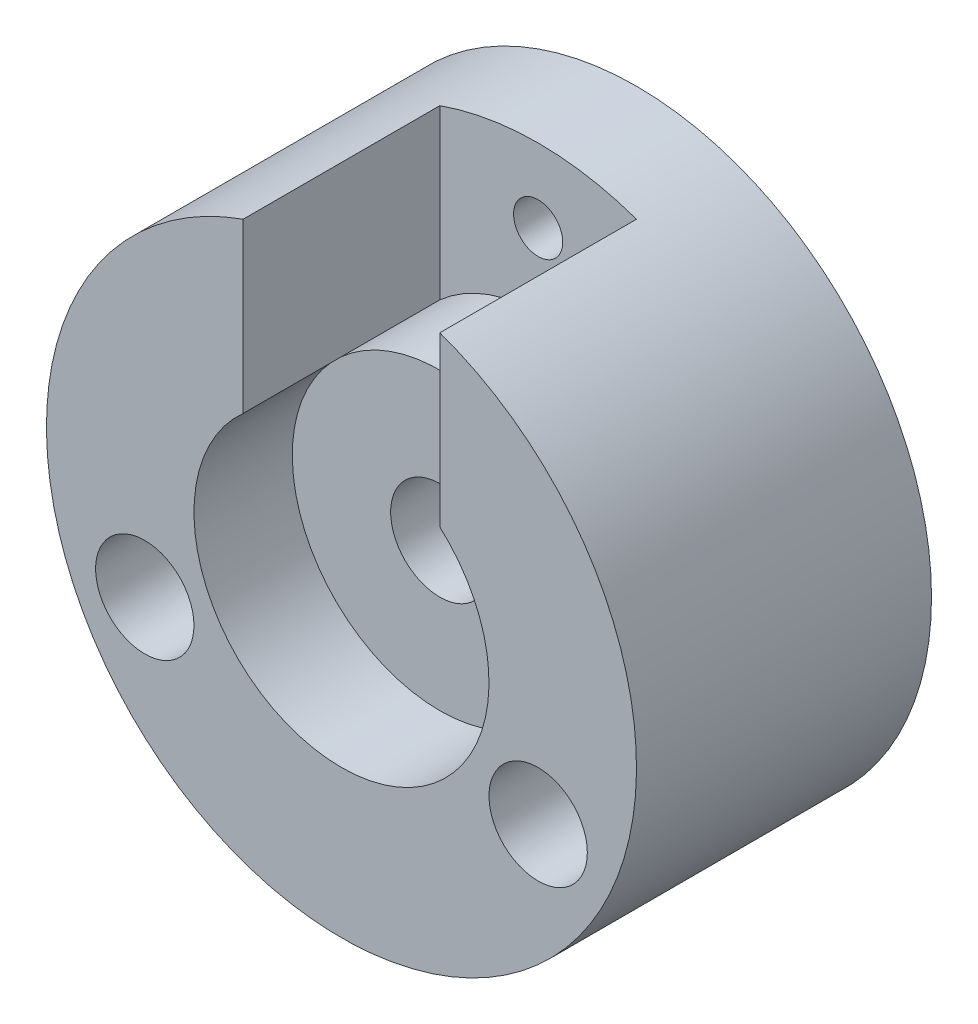
SolidWorks part; units mm, degrees
ref_plane "Front Plane" through (0, 0, 0) normal (0, 0, 1) x (1, 0, 0)
ref_plane "Top Plane" through (0, 0, 0) normal (0, 1, 0) x (1, 0, 0)
ref_plane "Right Plane" through (0, 0, 0) normal (1, 0, 0) x (0, 0, -1)
sketch "Sketch1" plane through (0, 0, 0) normal (0, 0, 1) x (1, 0, 0)
  circle A0 centre (0, 0) radius 30
  dimension "D1" = 60
extrude "Boss-Extrude1" add sketch "Sketch1" along normal blind 30
sketch "Sketch2" plane through (0, 0, 30) normal (0, 0, 1) x (1, 0, 0)
  circle A0 centre (0, 0) radius 15
  dimension "D1" = 30
extrude "Cut-Extrude1" cut sketch "Sketch2" against normal blind 10
sketch "Sketch3" plane through (0, 0, 20) normal (0, 0, 1) x (1, 0, 0)
  circle A0 centre (0, 0) radius 5
  dimension "D1" = 10
extrude "Cut-Extrude2" cut sketch "Sketch3" against normal blind 10
sketch "Sketch5" plane through (0, 0, 30) normal (0, 0, 1) x (1, 0, 0)
  circle A0 centre (20, -10) radius 5
  circle A1 centre (-20, -10) radius 5
  dimension "D1" = 10
  dimension "D4" = 10
  dimension "D2" = 20
  dimension "D3" = 10
  dimension "D5" = 20
extrude "Cut-Extrude5" cut sketch "Sketch5" against normal blind 110
sketch "Sketch6" plane through (0, 0, 30) normal (0, 0, 1) x (1, 0, 0)
  line L0 (-10, 28.2843) -> (-10, 11.1803)
  line L1 (10, 28.2843) -> (10, 11.1803)
  circle A0 centre (0, 0) radius 30 construction
  circle A1 centre (0, 0) radius 15 construction
  circle A2 centre (0, 0) radius 15 construction
  arc A3 (-10, 28.2843) -> (10, 28.2843) centre (0, 0) cw
  arc A4 (-10, 11.1803) -> (10, 11.1803) centre (0, 0) cw
  dimension "D2" = 30
  dimension "D3" = 15
  dimension "D1" = 20
extrude "Cut-Extrude6" cut sketch "Sketch6" against normal blind 20
sketch "Sketch7" plane through (0, 0, 10) normal (0, 0, 1) x (1, 0, 0)
  line L0 (10, 11.1803) -> (10, 28.2843) construction
  circle A0 centre (0, 22.5) radius 2.5
  dimension "D1" = 5
  dimension "D2" = 22.5
  dimension "D3" = 10
extrude "Cut-Extrude7" cut sketch "Sketch7" against normal blind 20
sketch "Sketch8" plane through (0, 0, 10) normal (0, 0, 1) x (1, 0, 0)
  circle A1 centre (0, 0) radius 5
  circle A2 centre (0, 0) radius 5
  point P0 (0, 0)
  dimension "D1" = 0
extrude "Cut-Extrude8" cut sketch "Sketch8" against normal blind 10 contours A2
sketch "Sketch9" plane through (0, 0, 0) normal (0, 0, -1) x (-1, 0, 0)
  circle A0 centre (0, 0) radius 10
  dimension "D1" = 20
extrude "Cut-Extrude9" cut sketch "Sketch9" against normal blind 10
